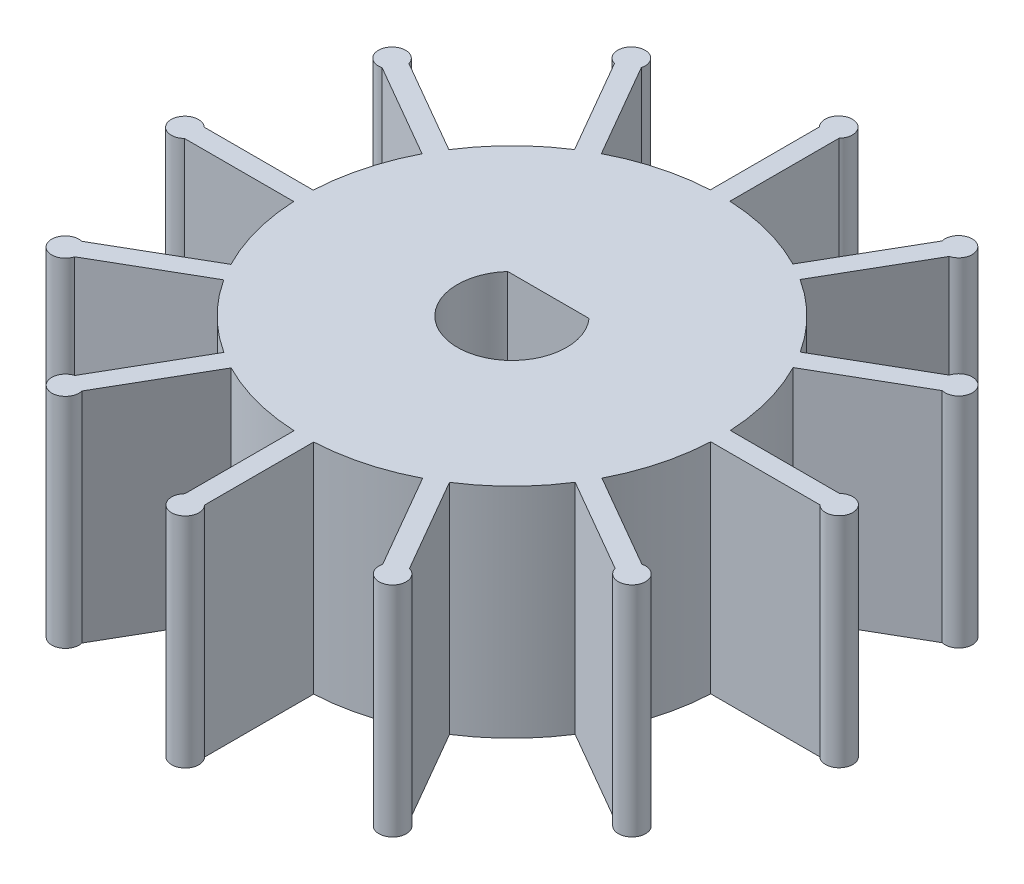
SolidWorks part; units mm, degrees
ref_plane "Front Plane" through (0, 0, 0) normal (0, 0, 1) x (1, 0, 0)
ref_plane "Top Plane" through (0, 0, 0) normal (0, 1, 0) x (1, 0, 0)
ref_plane "Right Plane" through (0, 0, 0) normal (1, 0, 0) x (0, 0, -1)
sketch "Sketch1" plane through (0, 0, 0) normal (0, 1, 0) x (1, 0, 0)
  line L9 (-0.5512, 17.4502) -> (-0.5512, 11.4502)
  line L10 (0.5275, 17.4502) -> (0.5275, 11.4514)
  line L11 (8.2478, 15.3879) -> (5.2478, 10.1918)
  line L12 (9.182, 14.8486) -> (6.1825, 9.6534)
  line L13 (14.8368, 9.2025) -> (9.6406, 6.2025)
  line L14 (15.3761, 8.2683) -> (10.1809, 5.2688)
  line L15 (17.4502, 0.5512) -> (11.4502, 0.5512)
  line L16 (17.4502, -0.5275) -> (11.4514, -0.5275)
  line L17 (15.3879, -8.2478) -> (10.1918, -5.2478)
  line L18 (14.8486, -9.182) -> (9.6534, -6.1825)
  line L19 (9.2025, -14.8368) -> (6.2025, -9.6406)
  line L20 (8.2683, -15.3761) -> (5.2688, -10.1809)
  line L21 (0.5512, -17.4502) -> (0.5512, -11.4502)
  line L22 (-0.5275, -17.4502) -> (-0.5275, -11.4514)
  line L23 (-8.2478, -15.3879) -> (-5.2478, -10.1918)
  line L24 (-9.182, -14.8486) -> (-6.1825, -9.6534)
  line L25 (-14.8368, -9.2025) -> (-9.6406, -6.2025)
  line L26 (-15.3761, -8.2683) -> (-10.1809, -5.2688)
  line L27 (-17.4502, -0.5512) -> (-11.4502, -0.5512)
  line L28 (-17.4502, 0.5275) -> (-11.4514, 0.5275)
  line L29 (-15.3879, 8.2478) -> (-10.1918, 5.2478)
  line L30 (-14.8486, 9.182) -> (-9.6534, 6.1825)
  line L31 (-9.2025, 14.8368) -> (-6.2025, 9.6406)
  line L32 (-8.2683, 15.3761) -> (-5.2688, 10.1809)
  arc A8 (5.2478, 10.1918) -> (0.5275, 11.4514) centre (0, 0) ccw
  arc A9 (0.5275, 17.4502) -> (-0.5512, 17.4502) centre (-0.0118, 17.9714) ccw
  arc A10 (9.182, 14.8486) -> (8.2478, 15.3879) centre (8.9754, 15.5696) ccw
  arc A11 (15.3761, 8.2683) -> (14.8368, 9.2025) centre (15.5578, 8.9959) ccw
  arc A12 (17.4502, -0.5275) -> (17.4502, 0.5512) centre (17.9714, 0.0118) ccw
  arc A13 (14.8486, -9.182) -> (15.3879, -8.2478) centre (15.5696, -8.9754) ccw
  arc A14 (8.2683, -15.3761) -> (9.2025, -14.8368) centre (8.9959, -15.5578) ccw
  arc A15 (-0.5275, -17.4502) -> (0.5512, -17.4502) centre (0.0118, -17.9714) ccw
  arc A16 (-9.182, -14.8486) -> (-8.2478, -15.3879) centre (-8.9754, -15.5696) ccw
  arc A17 (-15.3761, -8.2683) -> (-14.8368, -9.2025) centre (-15.5578, -8.9959) ccw
  arc A18 (-17.4502, 0.5275) -> (-17.4502, -0.5512) centre (-17.9714, -0.0118) ccw
  arc A19 (-14.8486, 9.182) -> (-15.3879, 8.2478) centre (-15.5696, 8.9754) ccw
  arc A20 (-8.2683, 15.3761) -> (-9.2025, 14.8368) centre (-8.9959, 15.5578) ccw
  arc A21 (9.6406, 6.2025) -> (6.1825, 9.6534) centre (0, 0) ccw
  arc A22 (11.4502, 0.5512) -> (10.1809, 5.2688) centre (0, 0) ccw
  arc A23 (-6.2025, 9.6406) -> (-9.6534, 6.1825) centre (0, 0) ccw
  arc A24 (-10.1918, 5.2478) -> (-11.4514, 0.5275) centre (0, 0) ccw
  arc A25 (-11.4502, -0.5512) -> (-10.1809, -5.2688) centre (0, 0) ccw
  arc A26 (-9.6406, -6.2025) -> (-6.1825, -9.6534) centre (0, 0) ccw
  arc A27 (-5.2478, -10.1918) -> (-0.5275, -11.4514) centre (0, 0) ccw
  arc A28 (0.5512, -11.4502) -> (5.2688, -10.1809) centre (0, 0) ccw
  arc A29 (6.2025, -9.6406) -> (9.6534, -6.1825) centre (0, 0) ccw
  arc A30 (10.1918, -5.2478) -> (11.4514, -0.5275) centre (0, 0) ccw
  arc A31 (-0.5512, 11.4502) -> (-5.2688, 10.1809) centre (0, 0) ccw
  point P1 (-11.373, 1.4372)
  point P2 (-16.5231, 8.6176)
  point P3 (-16.8734, 9.1162)
  point P5 (-16.502, 0.4376)
  point P10 (-16.5201, 0.768)
  point P53 (0, 0)
  point P68 (0, 0)
  point P69 (-16.5185, -0.3861)
  point P70 (-17.675, -0.1809)
  point P71 (-17.4502, -0.5512)
  dimension "D1" = 0.75
  dimension "D2" = 12
  dimension "D4" = 8
  dimension "D6" = 6
extrude "Boss-Extrude1" add sketch "Sketch1" along normal blind 12
sketch "Sketch2" plane through (0, 12, 0) normal (0, 1, 0) x (1, 0, 0)
  line L0 (-2.2361, 2) -> (2.2361, 2)
  arc A0 (-2.2361, 2) -> (2.2361, 2) centre (0, 0) ccw
  dimension "D1" = 3
  dimension "D2" = 2
extrude "Cut-Extrude1" cut sketch "Sketch2" against normal through all
